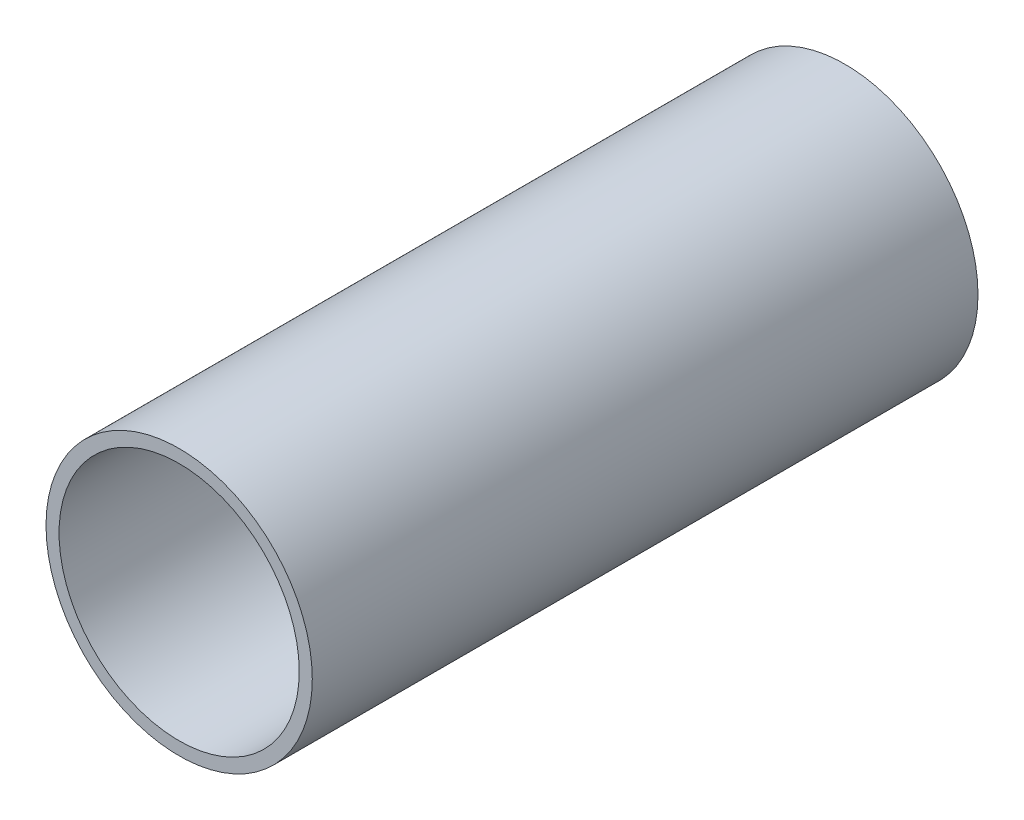
SolidWorks part; units mm, degrees
ref_plane "Top Plane" through (0, 0, 0) normal (0, 0, 1) x (1, 0, 0)
ref_plane "Front Plane" through (0, 0, 0) normal (0, 1, 0) x (1, 0, 0)
ref_plane "Right Plane" through (0, 0, 0) normal (1, 0, 0) x (0, 0, -1)
sketch "Profile Sketch" plane through (0, 0, 0) normal (0, 0, 1) x (1, 0, 0)
  circle A0 centre (0, 0) radius 11.4554
  circle A1 centre (0, 0) radius 12.7
  dimension "D1" = 25.4
  dimension "D2" = 22.9108
extrude "Profile Extrude" add sketch "Profile Sketch" along normal blind 63.5
